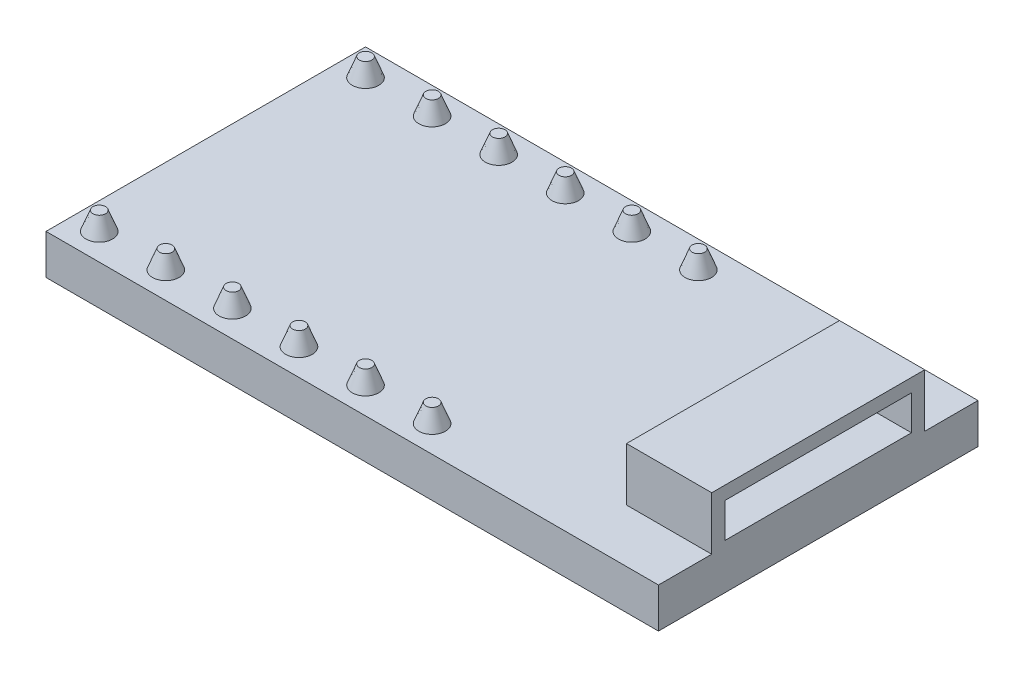
SolidWorks part; units mm, degrees
ref_plane "Front Plane" through (0, 0, 0) normal (0, 0, 1) x (1, 0, 0)
ref_plane "Top Plane" through (0, 0, 0) normal (0, 1, 0) x (1, 0, 0)
ref_plane "Right Plane" through (0, 0, 0) normal (1, 0, 0) x (0, 0, -1)
sketch "Sketch1" plane through (0, 0, 0) normal (0, 1, 0) x (1, 0, 0)
  line L1 (-11.5, -6) -> (11.5, -6)
  line L2 (-11.5, -6) -> (-11.5, 6)
  line L3 (-11.5, 6) -> (11.5, 6)
  line L4 (11.5, -6) -> (11.5, 6)
  line L5 (-11.5, -6) -> (11.5, 6) construction
  line L6 (-11.5, 6) -> (11.5, -6) construction
  point P0 (0, 0)
  dimension "D1" = 12
  dimension "D2" = 23
extrude "Boss-Extrude1" add sketch "Sketch1" along normal blind 1.5
sketch "Sketch2" plane through (0, 1.5, 0) normal (0, 1, 0) x (1, 0, 0)
  line L1 (11.5, -4) -> (8.3, -4)
  line L2 (11.5, -4) -> (11.5, 4)
  line L3 (11.5, 4) -> (8.3, 4)
  line L4 (8.3, -4) -> (8.3, 4)
  line L5 (11.5, -6) -> (11.5, 6) construction
  point P4 (10.8176, -3.8001)
  point P7 (11.5, 0)
  point P8 (11.5, 0)
  dimension "D1" = 8
  dimension "D2" = 3.2
extrude "Boss-Extrude2" add sketch "Sketch2" along normal blind 2
sketch "Sketch3" plane through (11.5, 0, 0) normal (1, 0, 0) x (0, 0, -1)
  line L0 (-4, 3.5) -> (4, 3.5) construction
  line L1 (-3.5, 3) -> (3.5, 3)
  line L2 (-3.5, 3) -> (-3.5, 1.7)
  line L3 (-3.5, 1.7) -> (3.5, 1.7)
  line L4 (3.5, 3) -> (3.5, 1.7)
  line L5 (-4, 3.5) -> (-4, 1.5) construction
  line L6 (-6, 1.5) -> (-4, 1.5) construction
  point P6 (0, 3.5)
  point P7 (0, 3)
  dimension "D1" = 0.5
  dimension "D2" = 0.5
  dimension "D3" = 0.2
extrude "Cut-Extrude1" cut sketch "Sketch3" against normal offset from surface (2.7 mm away) 0.5 up to face at (8.3, 2.5, 0)
sketch "Sketch4" plane through (0, 1.5, 0) normal (0, 1, 0) x (1, 0, 0)
  line L0 (-11.5, 6) -> (-11.5, -6) construction
  line L1 (11.5, 6) -> (-11.5, 6) construction
  circle A0 centre (-10.5, 5) radius 0.5
  dimension "D1" = 1
  dimension "D2" = 1
  dimension "D3" = 1
extrude "Boss-Extrude3" add sketch "Sketch4" along normal blind 0.69 draft 21
pattern_linear "LPattern1" count 6 spacing 2.5 along (1, 0, 0) of "Boss-Extrude3"
mirror "Mirror1" about plane through (0, 0, 0) normal (0, 0, 1) of "LPattern1", "Boss-Extrude3"
